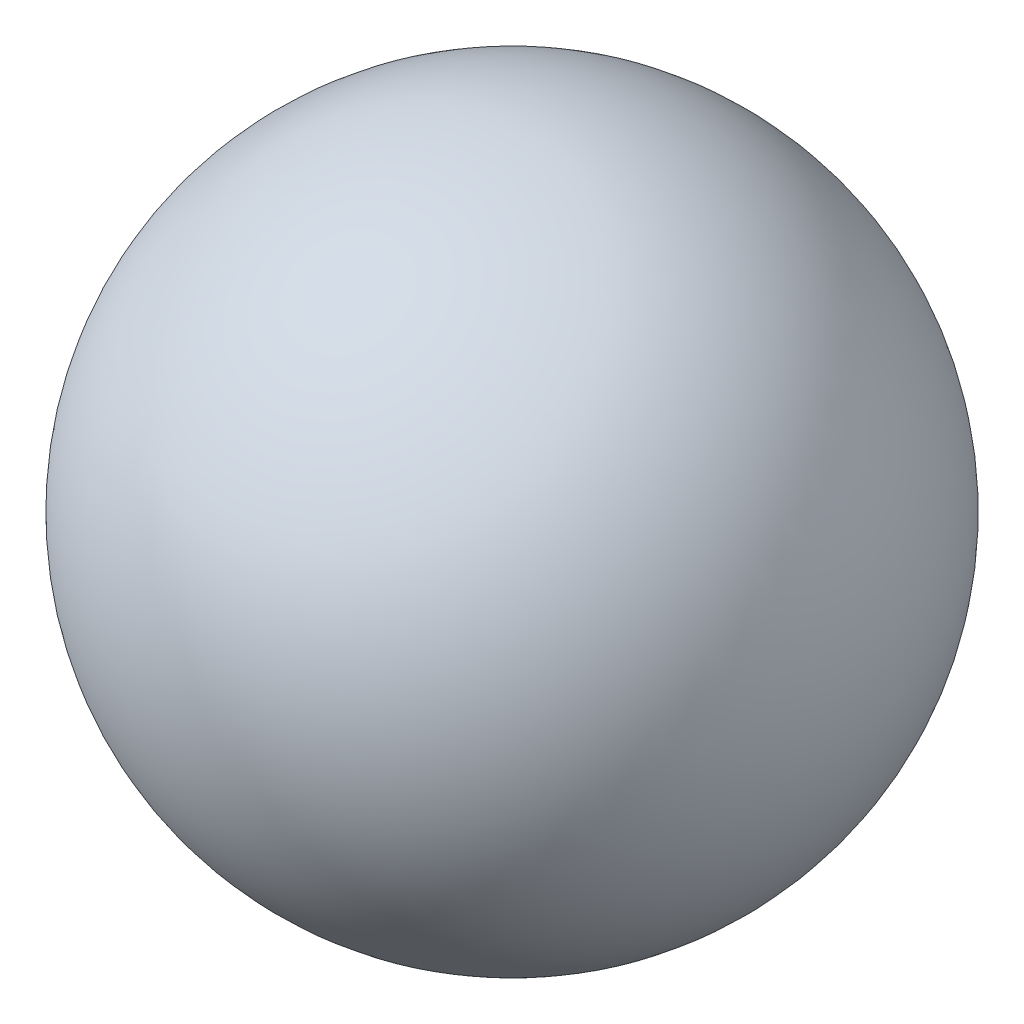
SolidWorks part; units mm, degrees
ref_plane "Front Plane" through (0, 0, 0) normal (0, 0, 1) x (1, 0, 0)
ref_plane "Top Plane" through (0, 0, 0) normal (0, 1, 0) x (1, 0, 0)
ref_plane "Right Plane" through (0, 0, 0) normal (1, 0, 0) x (0, 0, -1)
sketch "Sketch1" plane through (0, 0, 0) normal (0, 0, 1) x (1, 0, 0)
  line L0 (0, 31.5) -> (0, -31.5) construction
  line L1 (0, 31.5) -> (0, -31.5)
  arc A0 (0, 31.5) -> (0, -31.5) centre (0, 0) ccw
revolve "Revolve1" add sketch "Sketch1" angle 360 about L0
